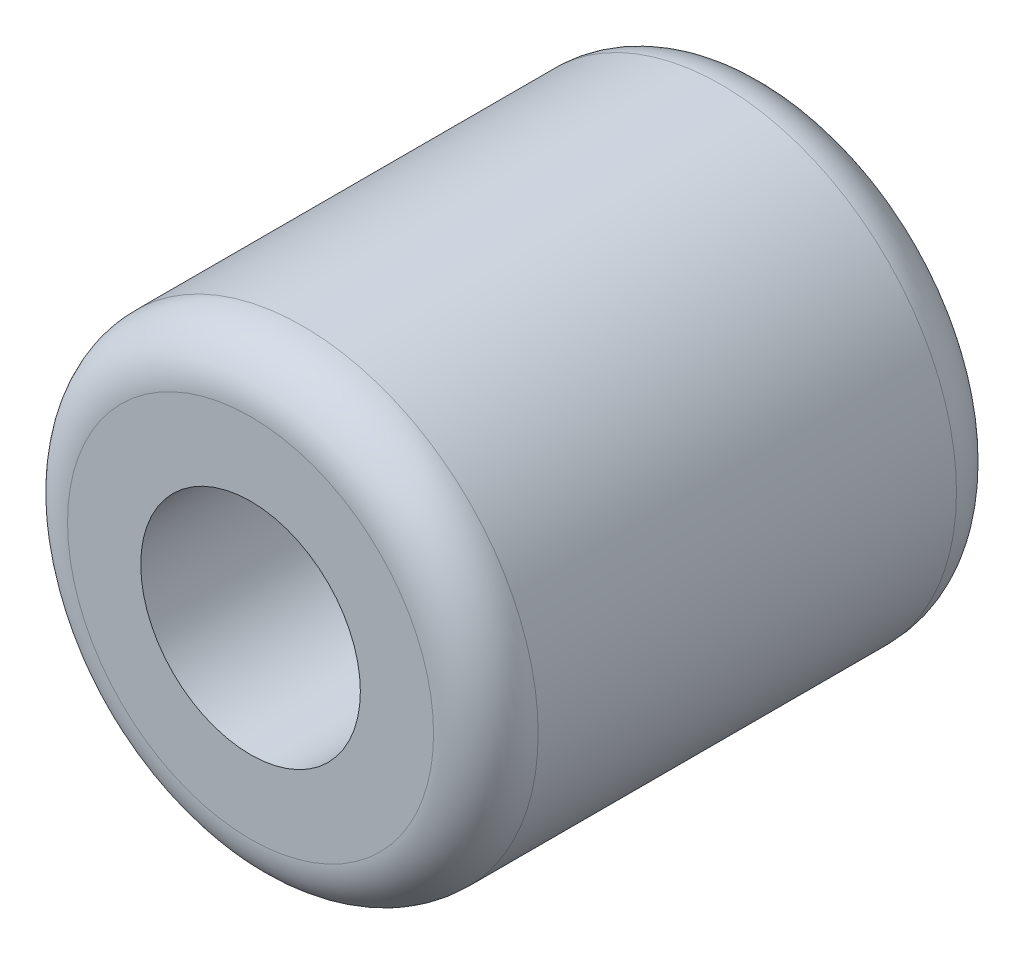
SolidWorks part; units mm, degrees
ref_plane "Ebene vorne" through (0, 0, 0) normal (0, 0, 1) x (1, 0, 0)
ref_plane "Ebene oben" through (0, 0, 0) normal (0, 1, 0) x (1, 0, 0)
ref_plane "Ebene rechts" through (0, 0, 0) normal (1, 0, 0) x (0, 0, -1)
sketch "Skizze1" plane through (0, 0, 0) normal (0, 0, 1) x (1, 0, 0)
  circle A0 centre (0, 0) radius 4.5
  circle A1 centre (0, 0) radius 2.1
  dimension "D1" = 9
  dimension "D2" = 4.2
extrude "Aufsatz-Linear austragen1" add sketch "Skizze1" along normal blind 10
fillet "Verrundung1" radius 1 2 edges at (4.5, 0, 0) (4.5, 0, 10)
